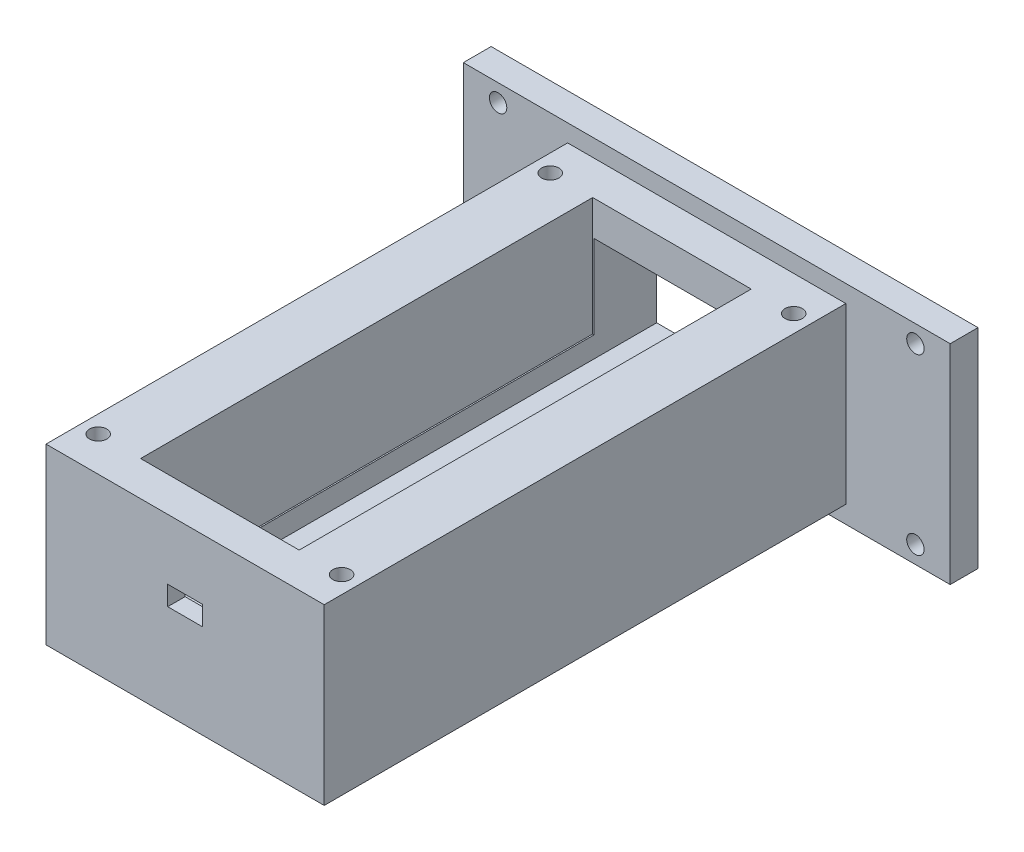
SolidWorks part; units mm, degrees
ref_plane "Front Plane" through (0, 0, 0) normal (0, 0, 1) x (1, 0, 0)
ref_plane "Top Plane" through (0, 0, 0) normal (0, 1, 0) x (1, 0, 0)
ref_plane "Right Plane" through (0, 0, 0) normal (1, 0, 0) x (0, 0, -1)
sketch "Sketch2" plane through (0, 0, 0) normal (0, 0, 1) x (1, 0, 0)
  line L1 (-23.789, 17.8125) -> (46.211, 17.8125)
  line L2 (-23.789, 17.8125) -> (-23.789, -12.1875)
  line L3 (-23.789, -12.1875) -> (46.211, -12.1875)
  line L4 (46.211, 17.8125) -> (46.211, -12.1875)
  dimension "D1" = 70
  dimension "D2" = 30
extrude "Boss-Extrude1" add sketch "Sketch2" along normal blind 4
sketch "Sketch4" plane through (0, 0, 4) normal (0, 0, 1) x (1, 0, 0)
  line L0 (-23.789, 17.8125) -> (-23.789, -12.1875) construction
  line L1 (-8.789, 15.3125) -> (31.211, 15.3125)
  line L2 (-8.789, 15.3125) -> (-8.789, -9.6875)
  line L3 (-8.789, -9.6875) -> (31.211, -9.6875)
  line L4 (31.211, 15.3125) -> (31.211, -9.6875)
  line L5 (46.211, 17.8125) -> (46.211, -12.1875) construction
  line L6 (-23.789, -12.1875) -> (46.211, -12.1875) construction
  line L7 (-23.789, 17.8125) -> (46.211, 17.8125) construction
  dimension "D1" = 15
  dimension "D2" = 15
  dimension "D3" = 25
  dimension "D4" = 2.5
  dimension "D5" = 2.5
extrude "Boss-Extrude7" add sketch "Sketch4" along normal blind 75
sketch "Sketch6" plane through (0, 0, 0) normal (0, 0, -1) x (-1, 0, 0)
  line L0 (-46.211, 17.8125) -> (-46.211, -12.1875) construction
  line L1 (-22.411, 10.3125) -> (-0.011, 10.3125)
  line L2 (-22.411, 10.3125) -> (-22.411, -4.6875)
  line L3 (-22.411, -4.6875) -> (-0.011, -4.6875)
  line L4 (-0.011, 10.3125) -> (-0.011, -4.6875)
  line L5 (23.789, 17.8125) -> (23.789, -12.1875) construction
  line L6 (23.789, 17.8125) -> (-46.211, 17.8125) construction
  line L7 (23.789, -12.1875) -> (-46.211, -12.1875) construction
  dimension "D1" = 23.8
  dimension "D2" = 23.8
  dimension "D3" = 7.5
  dimension "D4" = 7.5
extrude "Cut-Extrude13" cut sketch "Sketch6" against normal blind 76.5
sketch "Sketch8" plane through (0, 15.3125, 0) normal (0, 1, 0) x (1, 0, 0)
  line L1 (-0.189, -9) -> (22.611, -9)
  line L2 (-0.189, -9) -> (-0.189, -74)
  line L3 (-0.189, -74) -> (22.611, -74)
  line L4 (22.611, -9) -> (22.611, -74)
  line L7 (31.211, -79) -> (31.211, -4) construction
  line L8 (-8.789, -79) -> (-8.789, -4) construction
  line L9 (31.211, -79) -> (-8.789, -79) construction
  line L10 (31.211, -4) -> (-8.789, -4) construction
  dimension "D1" = 22.8
  dimension "D2" = 65
  dimension "D3" = 8.6
  dimension "D4" = 8.6
  dimension "D5" = 5
  dimension "D6" = 22.8
  dimension "D7" = 5
  dimension "D8" = 65
extrude "Cut-Extrude14" cut sketch "Sketch8" against normal blind 17
sketch "Sketch9" plane through (0, 15.3125, 0) normal (0, 1, 0) x (1, 0, 0)
  line L0 (31.211, -79) -> (31.211, -4) construction
  line L1 (22.611, -74) -> (22.611, -9) construction
  line L2 (-8.789, -79) -> (-8.789, -4) construction
  line L3 (31.211, -4) -> (-8.789, -4) construction
  line L4 (31.211, -79) -> (-8.789, -79) construction
  circle A0 centre (-6.289, -9) radius 1.25
  circle A1 centre (28.711, -9) radius 1.25
  circle A2 centre (-6.289, -74) radius 1.25
  circle A3 centre (28.711, -74) radius 1.25
  dimension "D4" = 2.5
  dimension "D5" = 2.5
  dimension "D7" = 2.5
  dimension "D9" = 2.5
  dimension "D1" = 8.6
  dimension "D2" = 2.5
  dimension "D3" = 2.5
  dimension "D6" = 2.5
  dimension "D8" = 2.5
  dimension "D10" = 5
  dimension "D11" = 5
  dimension "D12" = 5
  dimension "D13" = 5
extrude "Cut-Extrude15" cut sketch "Sketch9" against normal through all
sketch "Sketch10" plane through (0, -9.6875, 0) normal (0, -1, 0) x (1, 0, 0)
  line L5 (-8.789, 79) -> (31.211, 79) construction
  line L7 (31.211, 79) -> (31.211, 4) construction
  line L8 (-8.789, 79) -> (-8.789, 4) construction
  circle A0 centre (11.211, 59) radius 2.9
  dimension "D1" = 5.8
  dimension "D2" = 20
  dimension "D3" = 20
  dimension "D5" = 40
extrude "Cut-Extrude18" cut sketch "Sketch10" against normal blind 10
sketch "Sketch11" plane through (0, 0, 79) normal (0, 0, 1) x (1, 0, 0)
  line L0 (-8.789, 15.3125) -> (-8.789, -9.6875) construction
  line L1 (8.711, 6.6125) -> (13.711, 6.6125)
  line L2 (8.711, 6.6125) -> (8.711, 3.8125)
  line L3 (8.711, 3.8125) -> (13.711, 3.8125)
  line L4 (13.711, 6.6125) -> (13.711, 3.8125)
  line L6 (31.211, 15.3125) -> (-8.789, 15.3125) construction
  dimension "D1" = 5
  dimension "D2" = 2.8
  dimension "D3" = 17.5
  dimension "D4" = 8.7
extrude "Cut-Extrude17" cut sketch "Sketch11" against normal blind 10
sketch "Sketch12" plane through (0, 0, 0) normal (0, 0, -1) x (-1, 0, 0)
  line L0 (-41.211, 15.3125) -> (-41.211, 17.8125) construction
  line L1 (23.789, 17.8125) -> (-46.211, 17.8125) construction
  line L2 (-41.211, 15.3125) -> (-46.211, 15.3125) construction
  line L3 (-46.211, 17.8125) -> (-46.211, -12.1875) construction
  line L4 (-11.211, 17.8125) -> (-11.211, -12.1875) construction
  line L5 (23.789, -12.1875) -> (-46.211, -12.1875) construction
  line L6 (-46.211, 2.8125) -> (23.789, 2.8125) construction
  line L7 (23.789, 17.8125) -> (23.789, -12.1875) construction
  circle A0 centre (-41.211, 15.3125) radius 1.25
  circle A2 centre (18.789, 15.3125) radius 1.25
  circle A3 centre (18.789, -9.6875) radius 1.25
  circle A4 centre (-41.211, -9.6875) radius 1.25
  dimension "D1" = 2.5
  dimension "D2" = 2.5
  dimension "D3" = 5
extrude "Cut-Extrude20" cut sketch "Sketch12" against normal blind 10
